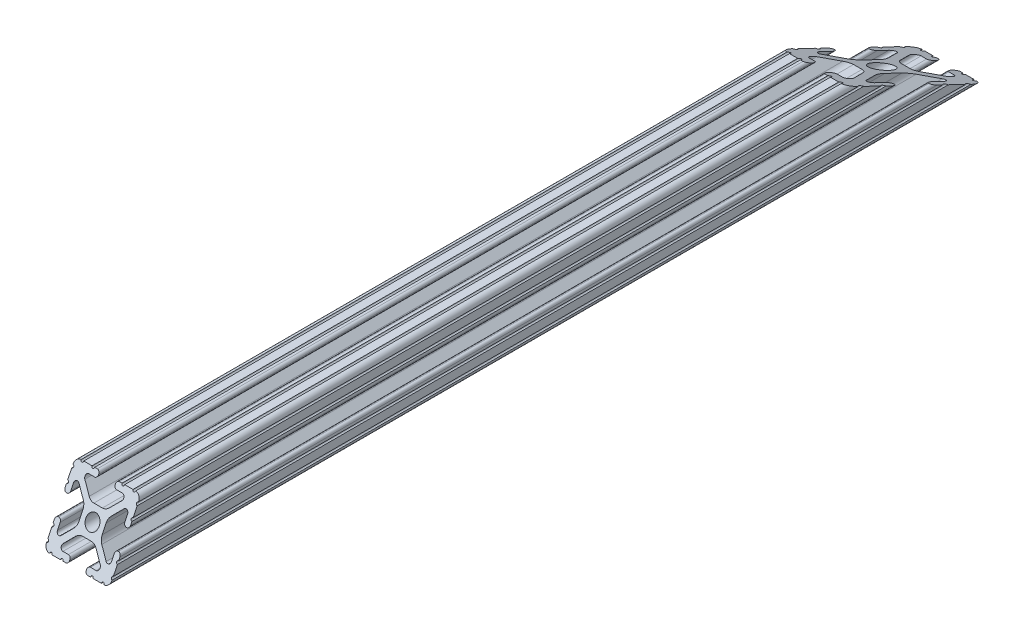
SolidWorks part; units mm, degrees
ref_plane "Front Plane" through (0, 0, 0) normal (0, 0, 1) x (1, 0, 0)
ref_plane "Top Plane" through (0, 0, 0) normal (0, 1, 0) x (1, 0, 0)
ref_plane "Right Plane" through (0, 0, 0) normal (1, 0, 0) x (0, 0, -1)
sketch "Sketch1" plane through (0, 0, 0) normal (0, 0, 1) x (1, 0, 0)
  line L88 (-7.1797, -8.6452) -> (-3.9523, -5.4237)
  line L89 (-1.7093, -4.4958) -> (1.7093, -4.4958)
  line L90 (3.9523, -5.4237) -> (7.1797, -8.6452)
  line L91 (6.4164, -10.4902) -> (4.2875, -10.4902)
  line L92 (3.2385, -11.5392) -> (3.2385, -11.651)
  line L93 (4.2875, -12.7) -> (5.3171, -12.7)
  line L94 (6.3331, -12.7) -> (9.5504, -12.7)
  line L95 (12.7, -9.5504) -> (12.7, -6.3331)
  line L96 (12.7, -5.3171) -> (12.7, -4.2875)
  line L97 (11.651, -3.2385) -> (11.5392, -3.2385)
  line L98 (10.4902, -4.2875) -> (10.4902, -6.4021)
  line L99 (8.7371, -7.1294) -> (5.441, -3.8408)
  line L100 (4.5085, -1.5932) -> (4.5085, 1.5932)
  line L101 (5.441, 3.8408) -> (8.7371, 7.1294)
  line L102 (10.4902, 6.4021) -> (10.4902, 4.2875)
  line L103 (11.5392, 3.2385) -> (11.651, 3.2385)
  line L104 (12.7, 4.2875) -> (12.7, 5.3171)
  line L105 (12.7, 6.3331) -> (12.7, 9.5504)
  line L106 (9.5504, 12.7) -> (6.3331, 12.7)
  line L107 (5.3171, 12.7) -> (4.2875, 12.7)
  line L108 (3.2385, 11.651) -> (3.2385, 11.5392)
  line L109 (4.2875, 10.4902) -> (6.4768, 10.4902)
  line L110 (7.207, 8.7244) -> (3.8983, 5.4232)
  line L111 (1.6558, 4.4958) -> (-1.6558, 4.4958)
  line L112 (-3.8983, 5.4232) -> (-7.207, 8.7244)
  line L113 (-6.4768, 10.4902) -> (-4.2875, 10.4902)
  line L114 (-3.2385, 11.5392) -> (-3.2385, 11.651)
  line L115 (-4.2875, 12.7) -> (-5.3171, 12.7)
  line L116 (-6.3331, 12.7) -> (-9.5504, 12.7)
  line L117 (-12.7, 9.5504) -> (-12.7, 6.3331)
  line L118 (-12.7, 5.3171) -> (-12.7, 4.2875)
  line L119 (-11.651, 3.2385) -> (-11.5392, 3.2385)
  line L120 (-10.4902, 4.2875) -> (-10.4902, 6.4021)
  line L121 (-8.7371, 7.1294) -> (-5.441, 3.8408)
  line L122 (-4.5085, 1.5932) -> (-4.5085, -1.5932)
  line L123 (-5.441, -3.8408) -> (-8.7371, -7.1294)
  line L124 (-10.4902, -6.4021) -> (-10.4902, -4.2875)
  line L125 (-11.5392, -3.2385) -> (-11.651, -3.2385)
  line L126 (-12.7, -4.2875) -> (-12.7, -5.3171)
  line L127 (-12.7, -6.3331) -> (-12.7, -9.5504)
  line L128 (-9.5504, -12.7) -> (-6.3331, -12.7)
  line L129 (-5.3171, -12.7) -> (-4.2875, -12.7)
  line L130 (-3.2385, -11.651) -> (-3.2385, -11.5392)
  line L131 (-4.2875, -10.4902) -> (-6.4164, -10.4902)
  circle A1 centre (0, 0) radius 2.6035
  arc A104 (-7.1797, -8.6452) -> (-6.4164, -10.4902) centre (-6.4164, -9.4098) ccw
  arc A105 (-1.7093, -4.4958) -> (-3.9523, -5.4237) centre (-1.7093, -7.6708) ccw
  arc A106 (3.9523, -5.4237) -> (1.7093, -4.4958) centre (1.7093, -7.6708) ccw
  arc A107 (6.4164, -10.4902) -> (7.1797, -8.6452) centre (6.4164, -9.4098) ccw
  arc A108 (4.2875, -10.4902) -> (3.2385, -11.5392) centre (4.2875, -11.5392) ccw
  arc A109 (3.2385, -11.651) -> (4.2875, -12.7) centre (4.2875, -11.651) ccw
  arc A110 (6.3331, -12.7) -> (5.3171, -12.7) centre (5.8251, -12.7) ccw
  arc A111 (10.5664, -12.6998) -> (9.5504, -12.7) centre (10.0584, -12.7) ccw
  arc A112 (10.5664, -12.6998) -> (12.6998, -10.5664) centre (10.5918, -10.5918) ccw
  arc A113 (12.7, -9.5504) -> (12.6998, -10.5664) centre (12.7, -10.0584) ccw
  arc A114 (12.7, -5.3171) -> (12.7, -6.3331) centre (12.7, -5.8251) ccw
  arc A115 (12.7, -4.2875) -> (11.651, -3.2385) centre (11.651, -4.2875) ccw
  arc A116 (11.5392, -3.2385) -> (10.4902, -4.2875) centre (11.5392, -4.2875) ccw
  arc A117 (8.7371, -7.1294) -> (10.4902, -6.4021) centre (9.4628, -6.4021) ccw
  arc A118 (4.5085, -1.5932) -> (5.441, -3.8408) centre (7.6835, -1.5932) ccw
  arc A119 (5.441, 3.8408) -> (4.5085, 1.5932) centre (7.6835, 1.5932) ccw
  arc A120 (10.4902, 6.4021) -> (8.7371, 7.1294) centre (9.4628, 6.4021) ccw
  arc A121 (10.4902, 4.2875) -> (11.5392, 3.2385) centre (11.5392, 4.2875) ccw
  arc A122 (11.651, 3.2385) -> (12.7, 4.2875) centre (11.651, 4.2875) ccw
  arc A123 (12.7, 6.3331) -> (12.7, 5.3171) centre (12.7, 5.8251) ccw
  arc A124 (12.6998, 10.5664) -> (12.7, 9.5504) centre (12.7, 10.0584) ccw
  arc A125 (12.6998, 10.5664) -> (10.5664, 12.6998) centre (10.5918, 10.5918) ccw
  arc A126 (9.5504, 12.7) -> (10.5664, 12.6998) centre (10.0584, 12.7) ccw
  arc A127 (5.3171, 12.7) -> (6.3331, 12.7) centre (5.8251, 12.7) ccw
  arc A128 (4.2875, 12.7) -> (3.2385, 11.651) centre (4.2875, 11.651) ccw
  arc A129 (3.2385, 11.5392) -> (4.2875, 10.4902) centre (4.2875, 11.5392) ccw
  arc A130 (7.207, 8.7244) -> (6.4768, 10.4902) centre (6.4768, 9.4563) ccw
  arc A131 (1.6558, 4.4958) -> (3.8983, 5.4232) centre (1.6558, 7.6708) ccw
  arc A132 (-3.8983, 5.4232) -> (-1.6558, 4.4958) centre (-1.6558, 7.6708) ccw
  arc A133 (-6.4768, 10.4902) -> (-7.207, 8.7244) centre (-6.4768, 9.4563) ccw
  arc A134 (-4.2875, 10.4902) -> (-3.2385, 11.5392) centre (-4.2875, 11.5392) ccw
  arc A135 (-3.2385, 11.651) -> (-4.2875, 12.7) centre (-4.2875, 11.651) ccw
  arc A136 (-6.3331, 12.7) -> (-5.3171, 12.7) centre (-5.8251, 12.7) ccw
  arc A137 (-10.5664, 12.6998) -> (-9.5504, 12.7) centre (-10.0584, 12.7) ccw
  arc A138 (-10.5664, 12.6998) -> (-12.6998, 10.5664) centre (-10.5918, 10.5918) ccw
  arc A139 (-12.7, 9.5504) -> (-12.6998, 10.5664) centre (-12.7, 10.0584) ccw
  arc A140 (-12.7, 5.3171) -> (-12.7, 6.3331) centre (-12.7, 5.8251) ccw
  arc A141 (-12.7, 4.2875) -> (-11.651, 3.2385) centre (-11.651, 4.2875) ccw
  arc A142 (-11.5392, 3.2385) -> (-10.4902, 4.2875) centre (-11.5392, 4.2875) ccw
  arc A143 (-8.7371, 7.1294) -> (-10.4902, 6.4021) centre (-9.4628, 6.4021) ccw
  arc A144 (-4.5085, 1.5932) -> (-5.441, 3.8408) centre (-7.6835, 1.5932) ccw
  arc A145 (-5.441, -3.8408) -> (-4.5085, -1.5932) centre (-7.6835, -1.5932) ccw
  arc A146 (-10.4902, -6.4021) -> (-8.7371, -7.1294) centre (-9.4628, -6.4021) ccw
  arc A147 (-10.4902, -4.2875) -> (-11.5392, -3.2385) centre (-11.5392, -4.2875) ccw
  arc A148 (-11.651, -3.2385) -> (-12.7, -4.2875) centre (-11.651, -4.2875) ccw
  arc A149 (-12.7, -6.3331) -> (-12.7, -5.3171) centre (-12.7, -5.8251) ccw
  arc A150 (-12.6998, -10.5664) -> (-12.7, -9.5504) centre (-12.7, -10.0584) ccw
  arc A151 (-12.6998, -10.5664) -> (-10.5664, -12.6998) centre (-10.5918, -10.5918) ccw
  arc A152 (-9.5504, -12.7) -> (-10.5664, -12.6998) centre (-10.0584, -12.7) ccw
  arc A153 (-5.3171, -12.7) -> (-6.3331, -12.7) centre (-5.8251, -12.7) ccw
  arc A154 (-4.2875, -12.7) -> (-3.2385, -11.651) centre (-4.2875, -11.651) ccw
  arc A155 (-3.2385, -11.5392) -> (-4.2875, -10.4902) centre (-4.2875, -11.5392) ccw
extrude "Boss-Extrude1" add sketch "Sketch1" along normal mid plane 370
sketch "Sketch2" plane through (12.7, 0, 0) normal (1, 0, 0) x (0, 0, -1)
  line L1 (-118.8279, 119.9979) -> (155.5702, -12.6998) construction
  line L3 (-185, -10.5664) -> (-185, -12.7) construction
  line L5 (0, 0) -> (0, 23.6002) construction
  line L19 (-164.4646, 25.6283) -> (-188.1081, -23.2627)
  line L20 (-183, -12.6998) -> (-118.8279, 119.9979) construction
  line L21 (-188.1081, -23.2627) -> (-213.259, -11.0998)
  line L22 (-213.259, -11.0998) -> (-189.6155, 37.7912)
  line L23 (-189.6155, 37.7912) -> (-164.4646, 25.6283)
  line L24 (-185, -12.6998) -> (185, -12.6998) construction
  line L45 (76.3136, 25.6283) -> (208.8693, -38.475)
  line L46 (208.8693, -38.475) -> (239.8694, 25.6283)
  line L47 (239.8694, 25.6283) -> (107.3137, 89.7317)
  line L48 (107.3137, 89.7317) -> (76.3136, 25.6283)
  dimension "D1" = 147.4
  dimension "D2" = 304.8
  dimension "D3" = 2
  dimension "D4" = 90
ref_plane "Offset" through (37.7, 0, 0) normal (1, 0, 0) x (0, 0, -1)
sketch "Sketch3" plane through (37.7, 0, 0) normal (1, 0, 0) x (0, 0, -1)
  line L0 (0.0033, -1.5937) -> (0.0033, 22.0065) construction
  line L1 (-172.2967, -14.2936) -> (-86.2623, 133.1064) construction
  line L2 (166.2733, -14.2936) -> (-86.2623, 133.1064) construction
  line L4 (118.0434, 13.8572) -> (185.0033, 13.8572)
  line L5 (185.0033, -26.3058) -> (166.2733, -26.3058)
  line L6 (166.2733, -26.3058) -> (166.2733, -14.2936)
  line L7 (166.2733, -14.2936) -> (118.0434, 13.8572)
  line L8 (-184.9967, -29.1886) -> (-172.2967, -29.1886)
  line L9 (-172.2967, -29.1886) -> (-172.2967, -14.2936)
  line L10 (-157.4714, 11.1061) -> (-172.2967, -14.2936)
  line L11 (185.0033, 13.8572) -> (194.7393, 13.8572)
  line L12 (-184.9967, 16.7584) -> (-154.1723, 16.7584)
  line L13 (-154.1723, 16.7584) -> (-157.4714, 11.1061)
  line L14 (-184.9967, 16.7584) -> (-192.6247, 16.7584)
  line L15 (-192.6247, 16.7584) -> (-192.6247, -29.1886)
  line L16 (-192.6247, -29.1886) -> (-184.9967, -29.1886)
  line L17 (194.7393, 13.8572) -> (194.7393, -26.3058)
  line L18 (194.7393, -26.3058) -> (185.0033, -26.3058)
  dimension "D2" = 147.4
  dimension "D3" = 338.57
  dimension "D4" = 90
extrude "Cut-Extrude4" cut sketch "Sketch2" against normal through all and the other way through all
